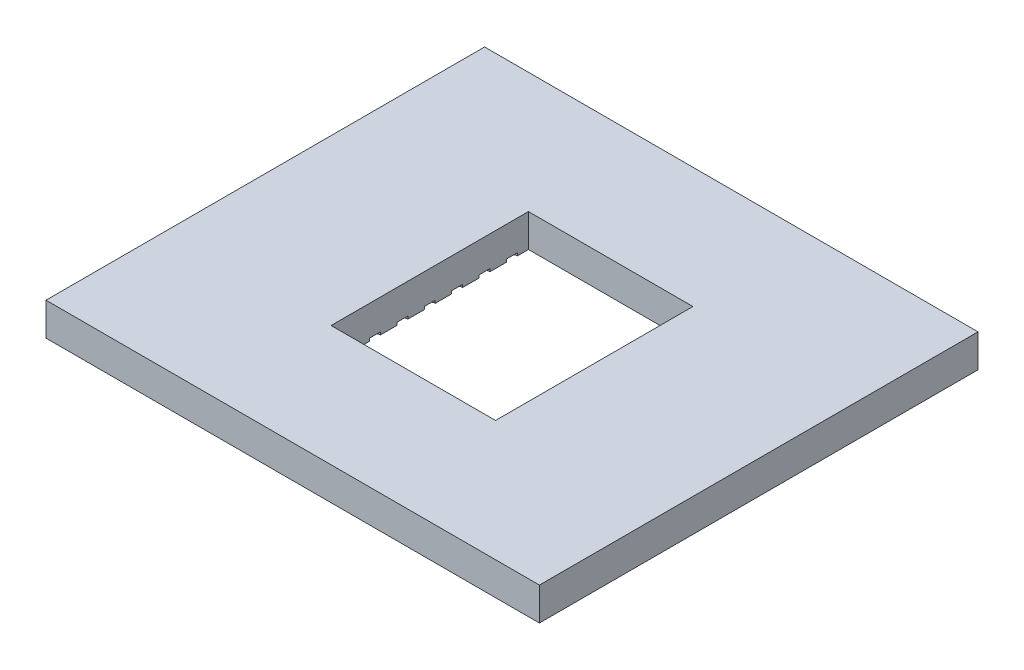
SolidWorks part; units mm, degrees
material "6061 Alloy"
ref_plane "Front Plane" through (0, 0, 0) normal (0, 0, 1) x (1, 0, 0)
ref_plane "Top Plane" through (0, 0, 0) normal (0, 1, 0) x (1, 0, 0)
ref_plane "Right Plane" through (0, 0, 0) normal (1, 0, 0) x (0, 0, -1)
sketch "Sketch1" plane through (0, 0, 0) normal (0, 1, 0) x (1, 0, 0)
  line L1 (-22.5, 20) -> (22.5, 20)
  line L2 (-22.5, 20) -> (-22.5, -20)
  line L3 (-22.5, -20) -> (22.5, -20)
  line L4 (22.5, 20) -> (22.5, -20)
  line L5 (-22.5, 20) -> (22.5, -20) construction
  line L6 (-22.5, -20) -> (22.5, 20) construction
  point P0 (0, 0)
  dimension "D1" = 40
  dimension "D2" = 45
extrude "Boss-Extrude1" add sketch "Sketch1" along normal blind 3
sketch "Sketch2" plane through (0, 0, 0) normal (0, -1, 0) x (1, 0, 0)
  line L0 (-20.5, 18) -> (20.5, 18)
  line L1 (-18.5, 16) -> (18.5, 16)
  line L2 (-18.5, 16) -> (-18.5, -16)
  line L3 (-18.5, -16) -> (18.5, -16)
  line L4 (18.5, 16) -> (18.5, -16)
  line L5 (-18.5, 16) -> (18.5, -16) construction
  line L6 (-18.5, -16) -> (18.5, 16) construction
  line L7 (20.5, 18) -> (20.5, -18)
  line L8 (-20.5, -18) -> (20.5, -18)
  line L9 (-20.5, 18) -> (-20.5, -18)
  point P0 (0, 0)
  dimension "D1" = 32
  dimension "D2" = 37
  dimension "D3" = 2
extrude "Cut-Extrude1" cut sketch "Sketch2" against normal blind 1
sketch "Sketch3" plane through (0, 0, 0) normal (0, -1, 0) x (-1, 0, 0)
  line L1 (7.5, -9) -> (-7.5, -9)
  line L2 (7.5, -9) -> (7.5, 9)
  line L3 (7.5, 9) -> (-7.5, 9)
  line L4 (-7.5, -9) -> (-7.5, 9)
  line L5 (7.5, -9) -> (-7.5, 9) construction
  line L6 (7.5, 9) -> (-7.5, -9) construction
  point P0 (0, 0)
  dimension "D1" = 18
  dimension "D2" = 15
extrude "Cut-Extrude2" cut sketch "Sketch3" against normal up to next
sketch "Sketch4" plane through (0, 0, 0) normal (0, -1, 0) x (-1, 0, 0)
  line L1 (12.5, -12.5) -> (-12.5, -12.5)
  line L2 (12.5, -12.5) -> (12.5, 12.5)
  line L3 (12.5, 12.5) -> (-12.5, 12.5)
  line L4 (-12.5, -12.5) -> (-12.5, 12.5)
  line L5 (12.5, -12.5) -> (-12.5, 12.5) construction
  line L6 (12.5, 12.5) -> (-12.5, -12.5) construction
  circle A0 centre (12.5, -12.5) radius 0.5
  point P0 (0, 0)
  dimension "D3" = 1
  dimension "D1" = 25
  dimension "D2" = 25
extrude "Cut-Extrude4" cut sketch "Sketch4" against normal blind 0.25 contours L1 A0 L2 | L2 A0 L1
pattern_linear "Glue Surface" count 11 spacing 2.5 along (1, 0, 0) count 11 spacing 2.5 along (0, 0, -1) of "Cut-Extrude4"
equation "\"2.5.00mm\"=50"
